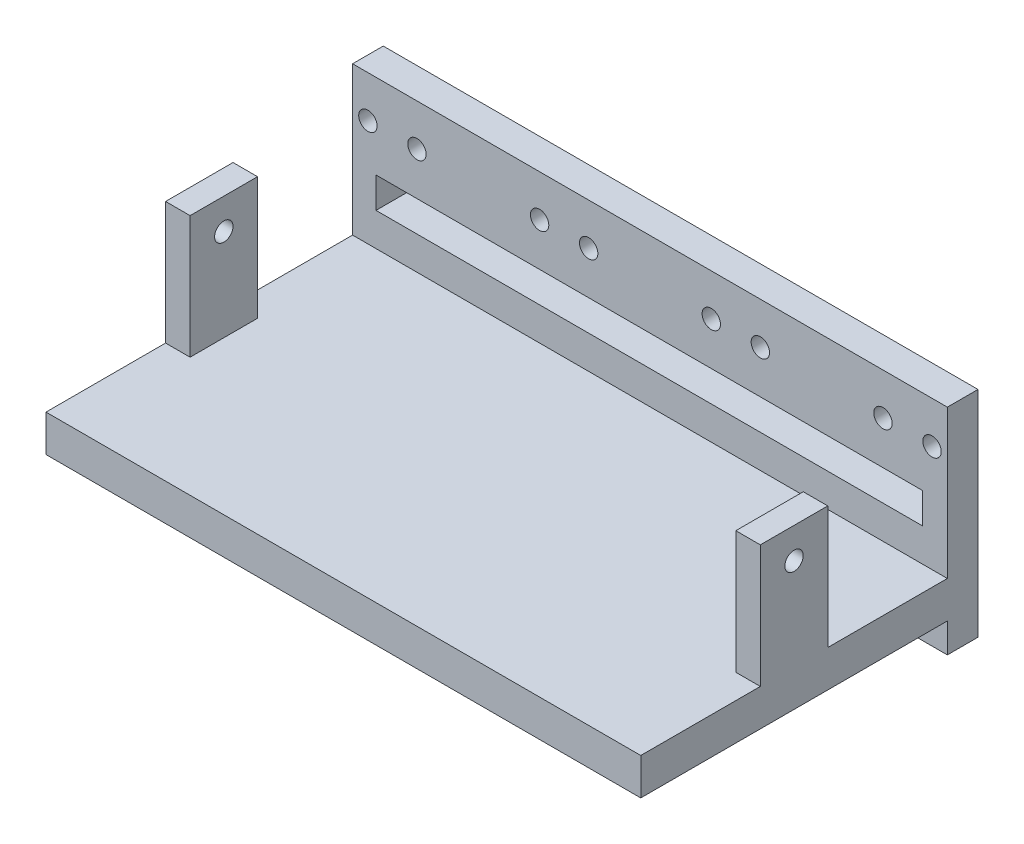
SolidWorks part; units mm, degrees
ref_plane "Front Plane" through (0, 0, 0) normal (0, 0, 1) x (1, 0, 0)
ref_plane "Top Plane" through (0, 0, 0) normal (0, 1, 0) x (1, 0, 0)
ref_plane "Right Plane" through (0, 0, 0) normal (1, 0, 0) x (0, 0, -1)
sketch "Sketch1" plane through (0, 0, 0) normal (0, 0, 1) x (1, 0, 0)
  line L0 (0, 15) -> (0, -6) construction
  line L1 (-48.5, -15) -> (48.5, -15)
  line L2 (-48.5, -15) -> (-48.5, 15)
  line L3 (-48.5, 15) -> (48.5, 15)
  line L4 (48.5, -15) -> (48.5, 15)
  line L5 (-48.5, -15) -> (48.5, 15) construction
  line L6 (-48.5, 15) -> (48.5, -15) construction
  circle A0 centre (-46, 13.2) radius 1.5
  circle A1 centre (-38, 13.2) radius 1.5
  circle A2 centre (-18, 13.2) radius 1.5
  circle A3 centre (-10, 13.2) radius 1.5
  circle A4 centre (10, 13.2) radius 1.5
  circle A5 centre (18, 13.2) radius 1.5
  circle A6 centre (38, 13.2) radius 1.5
  circle A7 centre (46, 13.2) radius 1.5
  point P0 (0, 0)
  dimension "D3" = 1.8
  dimension "D5" = 8
  dimension "D6" = 20
  dimension "D7" = 8
  dimension "D1" = 97
  dimension "D2" = 30
  dimension "D4" = 2.5
  dimension "D8" = 10
extrude "Boss-Extrude1" add sketch "Sketch1" against normal blind 5
sketch "Sketch2" plane through (0, -15, 0) normal (0, -1, 0) x (1, 0, 0)
  line L7 (-48.5, 0) -> (-48.5, -5)
  line L8 (-48.5, -5) -> (-27.9, -5)
  line L9 (-48.5, 0) -> (-27.9, 0)
  line L10 (-27.9, 0) -> (-27.9, -5)
  dimension "D1" = 20.6
extrude "Boss-Extrude2" add sketch "Sketch2" along normal blind 10
sketch "Sketch3" plane through (-48.5, 0, 0) normal (-1, 0, 0) x (0, 0, 1)
  line L0 (0, -25) -> (-5, -25)
  line L4 (-5, -25) -> (0, -23.7851)
  line L5 (0, 15) -> (0, -25) construction
  line L6 (0, -23.7851) -> (0, -25)
extrude "Cut-Extrude1" cut sketch "Sketch3" against normal up to next and the other way through all
sketch "Sketch4" plane through (-48.5, 0, 0) normal (-1, 0, 0) x (0, 0, 1)
  line L0 (0, -23.7851) -> (-1.1175, -24.0566)
  line L1 (-5, -25) -> (0, -23.7851) construction
  line L4 (-1.1175, -24.0566) -> (-0.1616, -27.9906)
  line L5 (-0.1616, -27.9906) -> (0, -23.7851)
  dimension "D1" = 1.15
extrude "Boss-Extrude3" add sketch "Sketch4" against normal blind 20.6
sketch "Sketch5" plane through (0, -22.459, 5.4572) normal (0, -0.9717, 0.2361) x (1, 0, 0)
  line L0 (-48.5, -10.7615) -> (-27.9, -10.7615) construction
  line L1 (-32.9, -10.7615) -> (-44.9, -10.7615)
  line L2 (-32.9, -10.7615) -> (-32.9, -6.766)
  line L3 (-32.9, -6.766) -> (-44.9, -6.766)
  line L4 (-44.9, -10.7615) -> (-44.9, -6.766)
  line L5 (-32.9, -10.7615) -> (-44.9, -6.766) construction
  line L6 (-32.9, -6.766) -> (-44.9, -10.7615) construction
  line L7 (-27.9, -6.766) -> (-48.5, -6.766) construction
  point P4 (-38.9, -8.7638)
  dimension "D1" = 5
  dimension "D2" = 3.6
extrude "Boss-Extrude4" add sketch "Sketch5" along normal through all
sketch "Sketch6" plane through (0, -1.5976, -6.5747) normal (0, -0.2361, -0.9717) x (-1, 0, 0)
  line L0 (48.5, -23.1125) -> (44.9, -23.1125) construction
  circle A0 centre (46.6342, -25.4125) radius 1.6
  dimension "D2" = 2.3
extrude "Cut-Extrude3" cut sketch "Sketch6" against normal blind 2
sketch "Sketch7" plane through (0, 0, 0) normal (0, 0, 1) x (1, 0, 0)
  line L0 (-48.5, 15) -> (48.5, 15)
  line L1 (-48.5, 15) -> (-48.5, 20)
  line L2 (48.5, 15) -> (48.5, 20)
  line L3 (-48.5, 20) -> (48.5, 20)
  dimension "D1" = 5
extrude "Boss-Extrude5" add sketch "Sketch7" against normal through all
sketch "Sketch8" plane through (0, 0, 0) normal (0, 0, 1) x (1, 0, 0)
  line L1 (-44.6801, 6.2) -> (44.4708, 6.2)
  line L2 (-44.6801, 6.2) -> (-44.6801, 1.2)
  line L3 (-44.6801, 1.2) -> (44.4708, 1.2)
  line L4 (44.4708, 6.2) -> (44.4708, 1.2)
  line L5 (-44.6801, 6.2) -> (44.4708, 1.2) construction
  line L6 (-44.6801, 1.2) -> (44.4708, 6.2) construction
  circle A0 centre (-46, 13.2) radius 1.5 construction
  point P4 (-0.1046, 3.7)
  point P5 (48.5, 1.2)
  point P11 (0, 0)
  dimension "D1" = 7
  dimension "D2" = 5
extrude "Cut-Extrude5" cut sketch "Sketch8" against normal through all
sketch "Sketch10" plane through (0, 0, 0) normal (0, 0, 1) x (1, 0, 0)
  line L0 (-48.5, 20) -> (-48.5, -23.7851) construction
  line L1 (-48.5, -4.1999) -> (48.5, -4.1999)
  line L2 (-48.5, -4.1999) -> (-48.5, -10.1999)
  line L3 (-48.5, -10.1999) -> (48.5, -10.1999)
  line L4 (48.5, -4.1999) -> (48.5, -10.1999)
  line L5 (-48.5, -4.1999) -> (48.5, -10.1999) construction
  line L6 (-48.5, -10.1999) -> (48.5, -4.1999) construction
  line L7 (48.5, -15) -> (48.5, 20) construction
  point P4 (0, -7.1999)
  dimension "D1" = 6
extrude "Boss-Extrude7" add sketch "Sketch10" along normal blind 50
sketch "Sketch11" plane through (0, -4.1999, 0) normal (0, 1, 0) x (1, 0, 0)
  line L0 (0, 0) -> (0, -50) construction
  line L1 (48.5, -19.5) -> (44.5, -19.5)
  line L2 (48.5, -19.5) -> (48.5, -30.5)
  line L3 (48.5, -30.5) -> (44.5, -30.5)
  line L4 (44.5, -19.5) -> (44.5, -30.5)
  line L5 (48.5, -19.5) -> (44.5, -30.5) construction
  line L6 (48.5, -30.5) -> (44.5, -19.5) construction
  line L7 (48.5, -50) -> (-48.5, -50) construction
  line L8 (-48.5, -30.5) -> (-44.5, -19.5) construction
  line L9 (-48.5, -19.5) -> (-44.5, -30.5) construction
  line L10 (-44.5, -19.5) -> (-44.5, -30.5)
  line L11 (-48.5, -30.5) -> (-44.5, -30.5)
  line L12 (-48.5, -19.5) -> (-44.5, -19.5)
  line L13 (-48.5, -19.5) -> (-48.5, -30.5)
  line L14 (48.5, -50) -> (48.5, 0) construction
  point P4 (46.5, -25)
  point P14 (-46.5, -25)
  point P15 (0, 0)
  dimension "D1" = 4
  dimension "D2" = 11
  dimension "D3" = 11
  dimension "D4" = 19.5
extrude "Boss-Extrude8" add sketch "Sketch11" along normal blind 20
sketch "Sketch12" plane through (-48.5, 0, 0) normal (-1, 0, 0) x (0, 0, 1)
  line L1 (19.5, 15.8001) -> (30.5, 15.8001) construction
  circle A0 centre (25, 10.8001) radius 1.5
  dimension "D1" = 5.5
  dimension "D2" = 5
extrude "Cut-Extrude6" cut sketch "Sketch12" against normal through all
